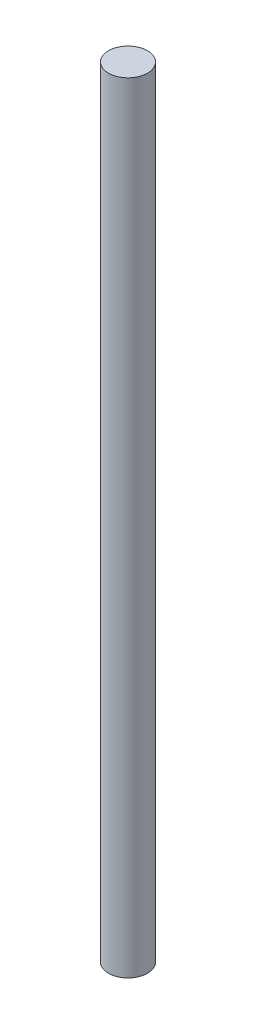
SolidWorks part; units mm, degrees
ref_plane "Front Plane" through (0, 0, 0) normal (0, 0, 1) x (1, 0, 0)
ref_plane "Top Plane" through (0, 0, 0) normal (0, 1, 0) x (1, 0, 0)
ref_plane "Right Plane" through (0, 0, 0) normal (1, 0, 0) x (0, 0, -1)
sketch "Sketch1" plane through (0, 0, 0) normal (0, 1, 0) x (1, 0, 0)
  circle A0 centre (0, 0) radius 1
  dimension "D1" = 2
extrude "Boss-Extrude1" add sketch "Sketch1" along normal blind 40
